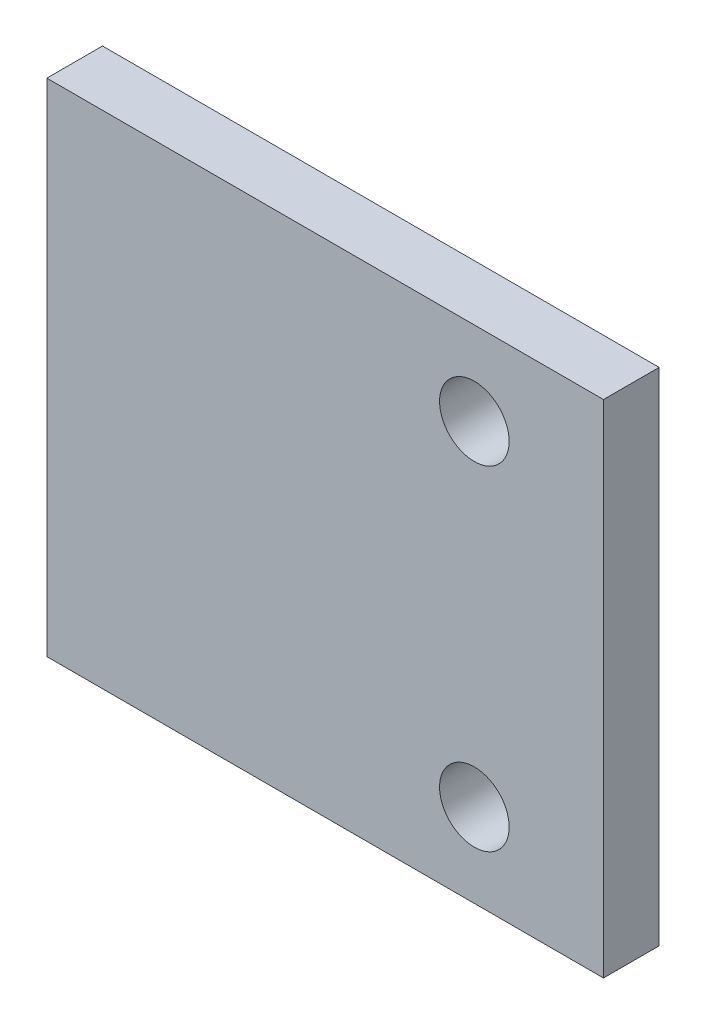
SolidWorks part; units mm, degrees
ref_plane "Plan de face" through (0, 0, 0) normal (0, 0, 1) x (1, 0, 0)
ref_plane "Plan de dessus" through (0, 0, 0) normal (0, 1, 0) x (1, 0, 0)
ref_plane "Plan de droite" through (0, 0, 0) normal (1, 0, 0) x (0, 0, -1)
sketch "Esquisse1" plane through (0, 0, 0) normal (0, 0, 1) x (1, 0, 0)
  line L0 (-7.7067, -4.1508) -> (12.2933, -4.1508) construction
  line L1 (-7.7067, 4.8492) -> (12.2933, 4.8492)
  line L2 (-7.7067, 4.8492) -> (-7.7067, -13.1508)
  line L3 (-7.7067, -13.1508) -> (12.2933, -13.1508)
  line L4 (12.2933, 4.8492) -> (12.2933, -13.1508)
  circle A0 centre (7.653, 1.8492) radius 1.25
  circle A1 centre (7.653, -10.1508) radius 1.25
  dimension "D4" = 2.5
  dimension "D5" = 2.5
  dimension "D1" = 20
  dimension "D2" = 18
  dimension "D3" = 12
  dimension "D6" = 6
extrude "Boss.-Extru.1" add sketch "Esquisse1" along normal blind 2
